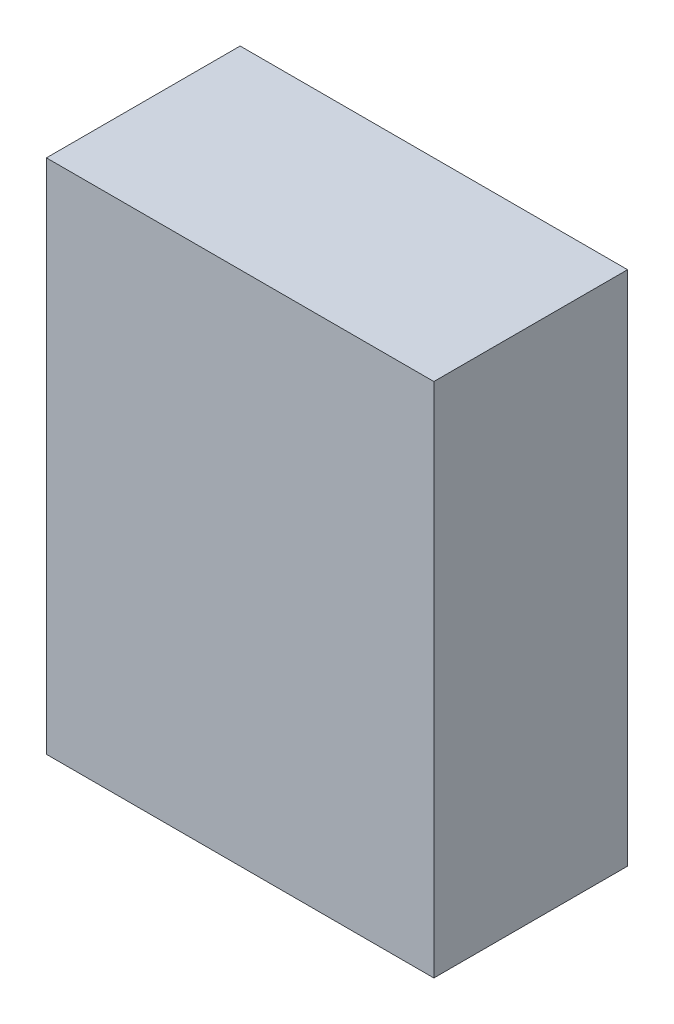
SolidWorks part; units mm, degrees
ref_plane "前基準面" through (0, 0, 0) normal (0, 0, 1) x (1, 0, 0)
ref_plane "上基準面" through (0, 0, 0) normal (0, 1, 0) x (1, 0, 0)
ref_plane "右基準面" through (0, 0, 0) normal (1, 0, 0) x (0, 0, -1)
sketch "草圖1" plane through (0, 0, 0) normal (0, 1, 0) x (1, 0, 0)
  line L1 (-750, 375) -> (750, 375)
  line L2 (-750, 375) -> (-750, -375)
  line L3 (-750, -375) -> (750, -375)
  line L4 (750, 375) -> (750, -375)
  line L5 (-750, 375) -> (750, -375) construction
  line L6 (-750, -375) -> (750, 375) construction
  point P0 (0, 0)
  dimension "D1" = 1500
  dimension "D2" = 750
extrude "填料-伸長1" add sketch "草圖1" along normal blind 2000
